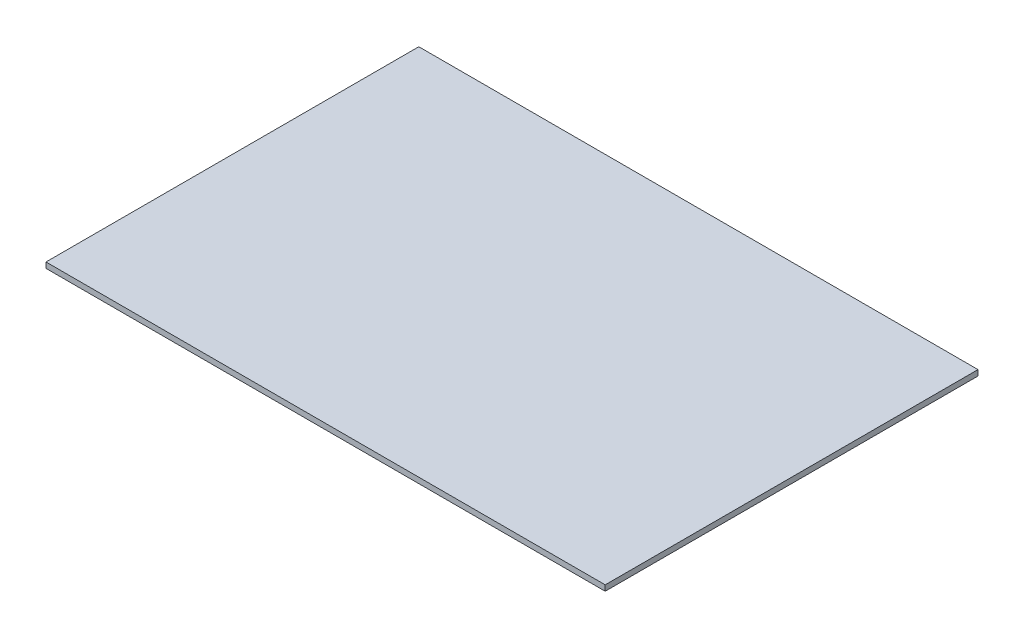
SolidWorks part; units mm, degrees
ref_plane "Front Plane" through (0, 0, 0) normal (0, 0, 1) x (1, 0, 0)
ref_plane "Top Plane" through (0, 0, 0) normal (0, 1, 0) x (1, 0, 0)
ref_plane "Right Plane" through (0, 0, 0) normal (1, 0, 0) x (0, 0, -1)
sketch "Sketch1" plane through (0, 0, 0) normal (0, 1, 0) x (1, 0, 0)
  line L1 (-150, 100) -> (150, 100)
  line L2 (-150, 100) -> (-150, -100)
  line L3 (-150, -100) -> (150, -100)
  line L4 (150, 100) -> (150, -100)
  line L5 (-150, 100) -> (150, -100) construction
  line L6 (-150, -100) -> (150, 100) construction
  point P0 (0, 0)
  dimension "D1" = 200
  dimension "D2" = 300
extrude "Boss-Extrude1" add sketch "Sketch1" along normal blind 3
